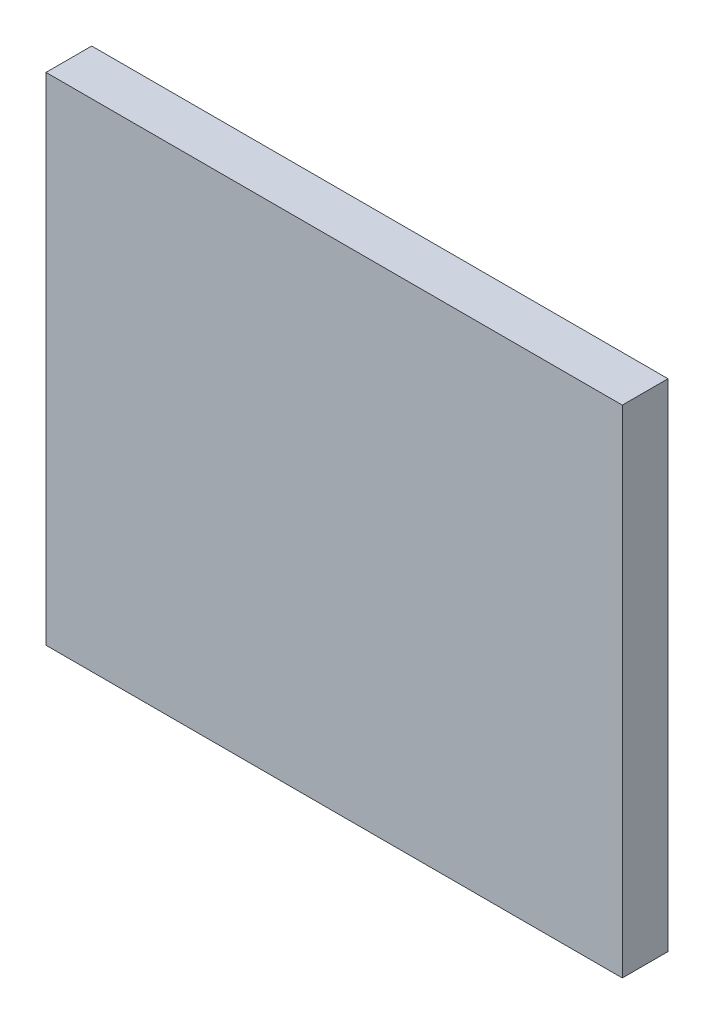
SolidWorks part; units mm, degrees
ref_plane "Front Plane" through (0, 0, 0) normal (0, 0, 1) x (1, 0, 0)
ref_plane "Top Plane" through (0, 0, 0) normal (0, 1, 0) x (1, 0, 0)
ref_plane "Right Plane" through (0, 0, 0) normal (1, 0, 0) x (0, 0, -1)
sketch "Sketch1" plane through (0, 0, 0) normal (0, 0, 1) x (1, 0, 0)
  line L1 (0, 0) -> (560.57, 0)
  line L2 (0, 0) -> (0, -482.6)
  line L3 (0, -482.6) -> (560.57, -482.6)
  line L4 (560.57, 0) -> (560.57, -482.6)
  dimension "D1" = 482.6
  dimension "D2" = 560.57
extrude "Boss-Extrude1" add sketch "Sketch1" along normal blind 44.45
ref_plane "Hinge Mirror Plane" through (280.285, 0, 0) normal (-1, 0, 0) x (0, 0, 1)
ref_plane "Hinge 2 Mirror Plane" through (356.7264, 0, 0) normal (1, 0, 0) x (0, 0, -1)
ref_plane "Plane3" through (0, -241.3, 0) normal (0, -1, 0) x (-1, 0, 0)
sketch "Sketch2" plane through (0, -241.3, 0) normal (0, -1, 0) x (-1, 0, 0)
  line L0 (-485.135, 0) -> (-485.135, -10)
  line L1 (0, 0) -> (-560.57, 0) construction
  line L2 (-485.135, 0) -> (-449.005, 0)
  line L3 (-449.005, 0) -> (-449.005, -10)
  line L4 (-391.635, -10) -> (-391.635, 0)
  line L5 (-391.635, 0) -> (-355.505, 0)
  line L6 (-355.505, 0) -> (-355.505, -10)
  line L7 (-560.57, -44.45) -> (-560.57, 0) construction
  arc A0 (-485.135, -10) -> (-449.005, -10) centre (-467.07, -3.9537) ccw
  arc A1 (-391.635, -10) -> (-355.505, -10) centre (-373.57, -3.9537) ccw
  dimension "D2" = 19.05
  dimension "D3" = 93.5
  dimension "D1" = 36.13
  dimension "D4" = 93.5
  dimension "D5" = 10
extrude "Cut-Extrude1" cut sketch "Sketch2" against normal blind 152.4 and the other way blind 152.4
mirror "Mirror1" about plane through (280.285, 0, 0) normal (-1, 0, 0) of "Cut-Extrude1"
